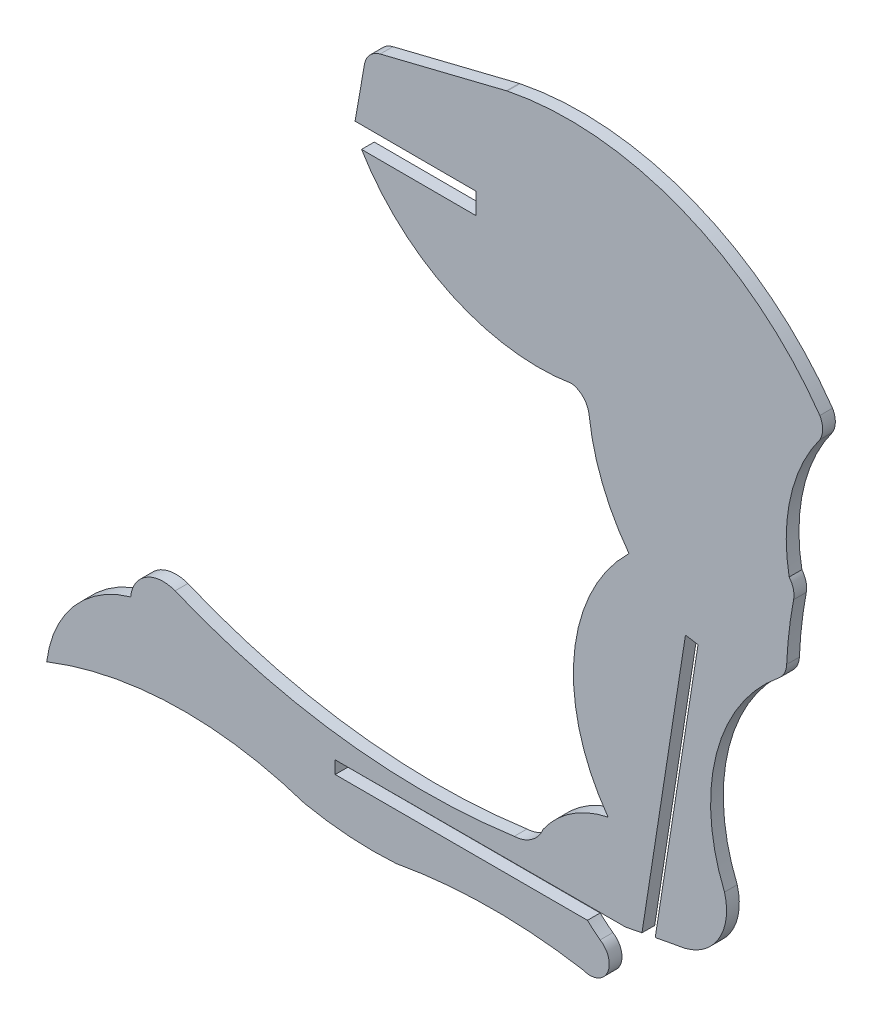
SolidWorks part; units mm, degrees
ref_plane "Front Plane" through (0, 0, 0) normal (0, 0, 1) x (1, 0, 0)
ref_plane "Top Plane" through (0, 0, 0) normal (0, 1, 0) x (1, 0, 0)
ref_plane "Right Plane" through (0, 0, 0) normal (1, 0, 0) x (0, 0, -1)
sketch "Sketch1" plane through (0, 0, 0) normal (0, 0, 1) x (1, 0, 0)
  line L0 (216.6727, -0.0074) -> (216.6727, -2.5474)
  line L1 (216.6727, -2.5474) -> (202.9229, -2.5276)
  line L2 (216.6727, -0.0074) -> (202.1482, 0.0136)
  line L3 (202.1482, 0.0136) -> (203.2698, 6.4639)
  line L4 (205.1614, 8.4942) -> (220.2914, 12.2433)
  line L5 (415.4863, -82.3745) -> (197.0188, -82.3745) construction
  line L6 (254.3833, -76.0279) -> (303.4816, -76.0279) construction
  line L7 (199.7618, -69.0114) -> (230.0045, -69.026)
  line L8 (199.7618, -67.4874) -> (234.5913, -67.4454)
  line L9 (199.7618, -69.0114) -> (199.7618, -67.4874)
  line L10 (236.6893, -71.0718) -> (242.5075, -33.6572) construction
  line L11 (241.7545, -33.5401) -> (243.2604, -33.7742)
  line L13 (238.1321, -66.753) -> (243.2604, -33.7742)
  line L14 (236.5421, -67.0594) -> (241.7545, -33.5401)
  arc A0 (254.7175, -23.3815) -> (254.1866, -21.2947) centre (252.2225, -22.9054) ccw
  arc A1 (202.9229, -2.5276) -> (228.1529, -14.2377) centre (224.1751, 10.2265) ccw
  arc A2 (230.0045, -69.026) -> (231.5288, -70.3025) centre (242.8008, -55.2934) ccw
  arc A3 (254.7175, -23.3815) -> (253.8883, -30.5187) centre (303.1559, -32.6262) ccw
  arc A4 (253.8883, -30.5187) -> (252.9449, -32.3875) centre (251.3506, -30.4101) cw
  arc A5 (252.9449, -32.3875) -> (246.4358, -57.8835) centre (266.7308, -49.4859) ccw
  arc A6 (246.4358, -57.8835) -> (241.6617, -66.0995) centre (240.0705, -59.6798) cw
  arc A7 (241.6617, -66.0995) -> (238.1321, -66.753) centre (305.3731, -420.0317) ccw
  arc A8 (231.5288, -70.3025) -> (229.4341, -74.4317) centre (230.2952, -72.2726) cw
  arc A9 (229.4341, -74.4317) -> (207.0855, -74.5959) centre (218.7257, -137.8894) ccw
  arc A10 (207.0855, -74.5959) -> (196.0883, -73.8489) centre (204.324, -33.9296) cw
  arc A11 (196.0883, -73.8489) -> (165.1799, -74.5959) centre (181.658, -116.5875) ccw
  arc A12 (165.1799, -74.5959) -> (175.2436, -62.8312) centre (179.067, -76.2884) cw
  arc A13 (175.2436, -62.8312) -> (180.5681, -59.5382) centre (179.1547, -63.204) cw
  arc A14 (180.5681, -59.5382) -> (221.2324, -64.6936) centre (210.3859, 12.7045) ccw
  arc A15 (224.6857, -62.2424) -> (221.2324, -64.6936) centre (221.0492, -60.7773) cw
  arc A16 (224.6857, -62.2424) -> (232.4794, -57.075) centre (235.0882, -69.4707) cw
  arc A17 (232.4794, -57.075) -> (234.9831, -28.46) centre (250.2821, -44.2156) cw
  arc A18 (234.9831, -28.46) -> (230.2019, -16.443) centre (254.8004, -13.6156) cw
  arc A19 (220.3921, 12.2661) -> (257.8622, -2.6822) centre (227.7641, -23.6913) cw
  arc A20 (236.5421, -67.0594) -> (234.5913, -67.4454) centre (305.3731, -420.0317) ccw
  arc A21 (228.1529, -14.2377) -> (230.2019, -16.443) centre (227.6785, -16.733) cw
  arc A22 (257.8622, -2.6822) -> (257.8749, -5.1784) centre (255.6564, -3.9416) cw
  arc A23 (257.8749, -5.1784) -> (254.1866, -21.2947) centre (274.6255, -17.4922) ccw
  arc A24 (203.2698, 6.4639) -> (205.1614, 8.4942) centre (205.7723, 6.0287) cw
  arc A25 (220.2914, 12.2433) -> (220.3921, 12.2661) centre (220.9023, 9.7779) cw
  point P48 (254.3833, -76.7899)
  point P49 (303.4816, -76.7899)
  point P50 (254.3833, -75.2659)
  point P51 (303.4816, -75.2659)
  point P56 (288.6923, -65.1275)
  point P58 (266.3502, -34.5573)
  point P59 (287.4619, -66.0268)
  point P60 (265.1198, -35.4565)
  dimension "D1" = 2.54
  dimension "D2" = 2.54
extrude "Boss-Extrude1" add sketch "Sketch1" along normal blind 1.524
